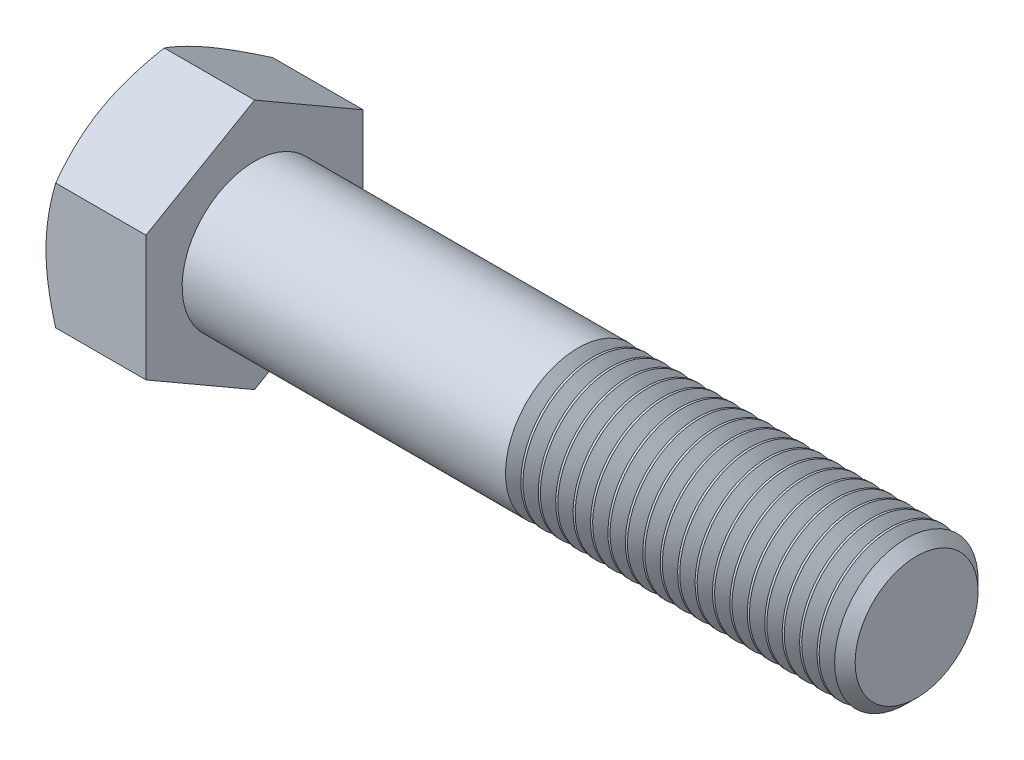
SolidWorks part; units mm, degrees
extrude "BaseHead" add sketch "Sketch1" along normal blind 15.3416
sketch "Sketch1" plane through (0, 0, 0) normal (1, 0, 0) x (0, 0, -1)
  line L0 (16.6624, 9.62) -> (16.6624, -9.62)
  line L1 (-16.6624, 9.62) -> (-16.6624, -9.62)
  line L2 (16.6624, -9.62) -> (0, -19.2401)
  line L3 (0, -19.2401) -> (-16.6624, -9.62)
  line L4 (16.6624, 9.62) -> (0, 19.2401)
  line L5 (0, 19.2401) -> (-16.6624, 9.62)
  dimension "Width_flats" = 33.3248
  dimension "D2" = 120
  dimension "D3" = 16.6624
  dimension "D4" = 16.6624
  dimension "D5" = 16.6624
ref_plane "Plane1" through (0, 0, 0) normal (0, 0, 1) x (1, 0, 0)
ref_plane "Plane2" through (0, 0, 0) normal (0, 1, 0) x (1, 0, 0)
ref_plane "Plane3" through (0, 0, 0) normal (1, 0, 0) x (0, 0, -1)
sketch "BodySke" plane through (0, 0, 0) normal (0, 0, 1) x (1, 0, 0)
  line L0 (0, 9.62) -> (0, -9.62) construction
  line L1 (0, 0) -> (116.9416, 0)
  line L2 (0, 0) -> (0, 11.1125)
  line L3 (0, 11.1125) -> (115.2614, 11.1125)
  line L4 (116.9416, 0) -> (116.9416, 9.4323)
  line L5 (15.3416, 19.2401) -> (15.3416, 9.62) construction
  line L6 (116.9416, 9.4323) -> (115.2614, 11.1125)
  line L7 (0, 0) -> (96.52, 0) construction
  line L8 (116.9416, -9.4323) -> (115.2614, -11.1125) construction
  line L9 (0, -11.1125) -> (115.2614, -11.1125) construction
  line L10 (18.1635, 15.24) -> (18.1635, -2.54) construction
  line L11 (66.1416, 15.24) -> (66.1416, -2.54) construction
  line L12 (15.3416, 9.62) -> (15.3416, -9.62) construction
  dimension "Diameter" = 22.225
revolve "BaseBody" add sketch "BodySke" angle 360 about L7
cosmetic thread "ThreadCosmetic" [suppressed] parameters "Thread_length"=50.8, "Thread_minor"=18.8646
sketch "Sketch3" plane through (0, 0, 0) normal (0, 0, 1) x (1, 0, 0)
  line L0 (0, 16.6624) -> (5.1544, 25.5901)
  line L1 (0, 19.2401) -> (0, 9.62) construction
  line L2 (5.1544, 25.5901) -> (5.1544, 31.9401)
  line L3 (5.1544, 31.9401) -> (-12.7, 31.9401)
  line L4 (-12.7, 31.9401) -> (-12.7, 16.6624)
  line L5 (-12.7, 16.6624) -> (0, 16.6624)
  line L6 (0, 0) -> (99.06, 0) construction
  line L7 (15.3416, 19.2401) -> (0, 19.2401) construction
  dimension "D1" = 16.6624
  dimension "D2" = 6.35
  dimension "D3" = 12.7
  dimension "D4" = 6.35
  dimension "Head_ch_ang" = 30
revolve "HeadChamfer" cut sketch "Sketch3" angle 360 about L6
fillet "HeadFillet" [suppressed] radius 1.524
sketch "ThdSchSke" plane through (0, 0, 0) normal (0, 0, 1) x (1, 0, 0)
  line L0 (66.1416, -9.4323) -> (64.9651, -11.1125)
  line L1 (66.1416, -9.4323) -> (67.3181, -11.1125)
  line L2 (67.3181, -11.1125) -> (67.3181, -13.8906)
  line L3 (-3.175, 0) -> (5.1513, 0) construction
  line L5 (67.3181, -13.8906) -> (64.9651, -13.8906)
  line L6 (64.9651, -13.8906) -> (64.9651, -11.1125)
  dimension "Thread_minor" = 18.8646
  dimension "Diameter" = 22.225
  dimension "Start" = 66.1416
revolve "ThreadSchematic" cut sketch "ThdSchSke" angle 360 about L3
pattern_linear "ThdSchPat" count 19 spacing 2.6737 along (1, 0, 0) of "ThreadSchematic"
equation "\"D3@Sketch1\" = \"Width_flats@Sketch1\" / 2"
equation "\"D4@Sketch1\" = \"D3@Sketch1\""
equation "\"D5@Sketch1\" = \"D4@Sketch1\""
equation "\"Thread_minor@ThreadCosmetic\" = \"Minor_dia@BodySke\""
equation "\"D1@Sketch3\" = \"Width_flats@Sketch1\" / 2"
equation "\"Thread_length@ThreadCosmetic\" = ((sgn( (\"Length@BodySke\" - \"Advance@BodySke\" ) - \"Thread_nom@BodySke\" )-1)*( (\"Length@BodySke\" - \"Advance@BodySke\" ) - \"Thread_nom@BodySke\" ))/-2+ \"Thread_nom@BodySke\""
equation "\"Thread_minor@ThdSchSke\" = \"Minor_dia@BodySke\""
equation "\"Diameter@ThdSchSke\" = \"Diameter@BodySke\""
equation "\"Overcut@ThdSchSke\" = \"Diameter@BodySke\" * 1.25"
equation "\"Start@ThdSchSke\" = \"Head_ht@BaseHead\" + \"Length@BodySke\" - \"Thread_length@ThreadCosmetic\"  '---Non-countersunk---"
equation "\"Num_threads@ThdSchPat\" = int( \"Thread_length@ThreadCosmetic\" / \"Advance@BodySke\" + 0.999 )  + 1"
equation "\"Advance@ThdSchPat\" = \"Thread_length@ThreadCosmetic\" /  (\"Num_threads@ThdSchPat\" - 1) 'relax it"
equation "\"Num_threads@ThdSchPat\" = \"Num_threads@ThdSchPat\" - sgn( \"Num_threads@ThdSchPat\" - 1) '---chamfered tips only---"
